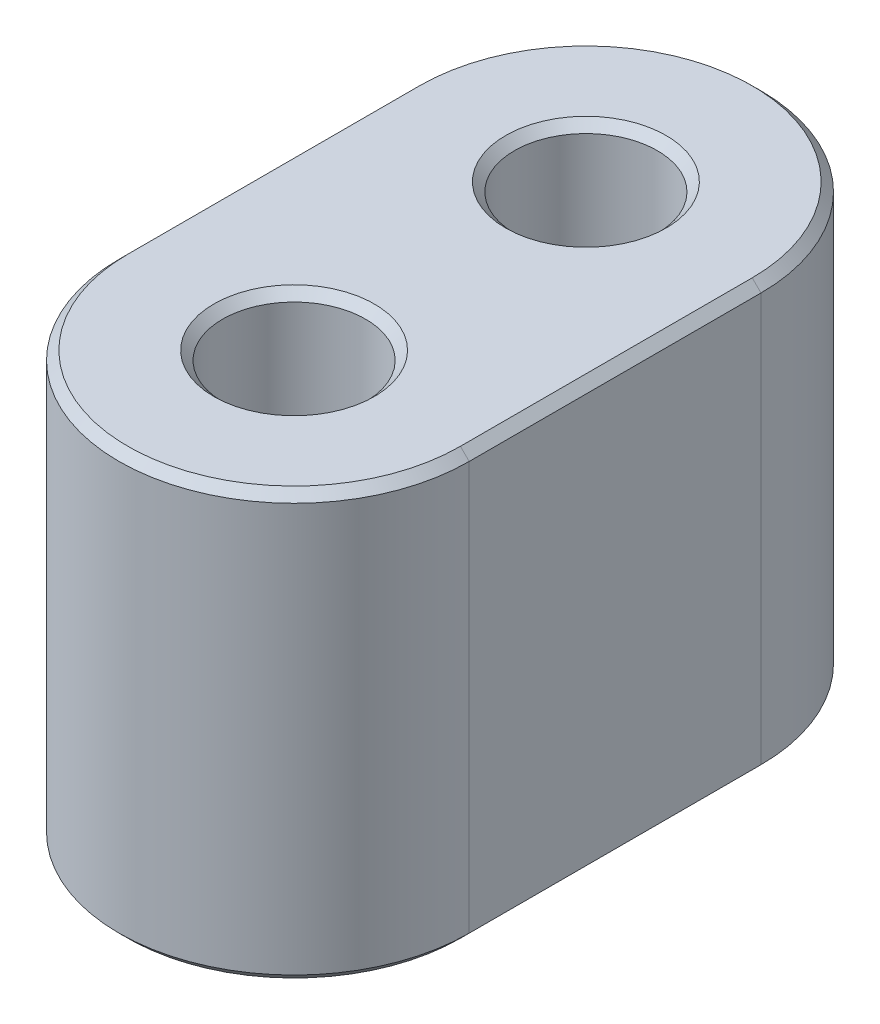
SolidWorks part; units mm, degrees
ref_plane "Front Plane (Z)" through (0, 0, 0) normal (0, 0, 1) x (1, 0, 0)
ref_plane "Top Plane (Y)" through (0, 0, 0) normal (0, 1, 0) x (1, 0, 0)
ref_plane "Side Plane (X)" through (0, 0, 0) normal (1, 0, 0) x (0, 0, -1)
sketch "Sketch1" plane through (0, 0, 0) normal (0, 1, 0) x (1, 0, 0)
  line L0 (0, 0) -> (0, 14.2703) construction
  line L1 (0, 0) -> (0, 10) construction
  line L2 (-6, 0) -> (-6, 10)
  line L3 (6, 0) -> (6, 10)
  circle A0 centre (0, 0) radius 2.45
  circle A1 centre (0, 10) radius 2.45
  arc A2 (-6, 0) -> (6, 0) centre (0, 0) ccw
  arc A3 (6, 10) -> (-6, 10) centre (0, 10) ccw
  point P6 (0, 5)
  dimension "D1" = 10
  dimension "D2" = 4.9
  dimension "D3" = 6
extrude "Boss-Extrude1" add sketch "Sketch1" along normal blind 14.6
chamfer "Chamfer1" distance 0.3 angle 45 12 edges at (0, 14.6, -7.55) (-6, 14.6, -5) (0, 14.6, -16) (6, 14.6, -5) (0, 14.6, 6) (0, 14.6, 2.45) (0, 0, -7.55) (0, 0, 2.45) (6, 0, -5) (0, 0, -16) (-6, 0, -5) (0, 0, 6)
